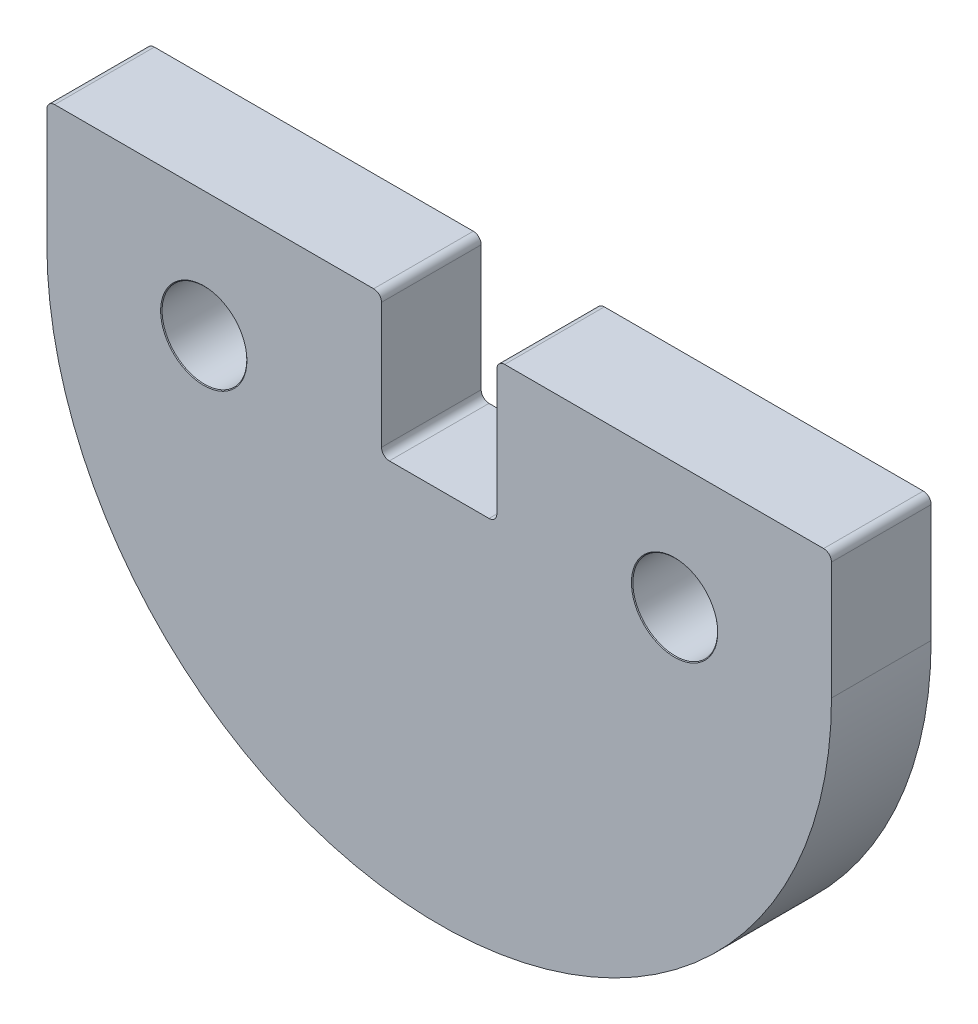
SolidWorks part; units mm, degrees
material "MDF"
ref_plane "Front Plane" through (0, 0, 0) normal (0, 0, 1) x (1, 0, 0)
ref_plane "Top Plane" through (0, 0, 0) normal (0, 1, 0) x (1, 0, 0)
ref_plane "Right Plane" through (0, 0, 0) normal (1, 0, 0) x (0, 0, -1)
sketch "Sketch1" plane through (0, 0, 0) normal (0, 0, 1) x (1, 0, 0)
  line L0 (-12.5, 0) -> (12.5, 0) construction
  line L1 (0, -1000) -> (0, 49000) construction
  line L2 (-12.5, 0) -> (12.5, 0) construction
  line L3 (-12.5, 0) -> (-12.5, 4)
  line L4 (-12.5, 4) -> (12.5, 4)
  line L5 (12.5, 0) -> (12.5, 4)
  line L7 (-1.8375, 4) -> (1.8375, 4)
  line L8 (-1.8375, 4) -> (-1.8375, -0.5)
  line L9 (-1.8375, -0.5) -> (1.8375, -0.5)
  line L10 (1.8375, 4) -> (1.8375, -0.5)
  arc A0 (-12.5, 0) -> (12.5, 0) centre (0, 0) ccw
  point P6 (-7.5, 0)
  point P7 (7.5, 0)
  dimension "D1" = 12.5
  dimension "D2" = 15
  dimension "D3" = 4
  dimension "D4" = 4.5
  dimension "D5" = 3.675
extrude "Boss-Extrude1" add sketch "Sketch1" along normal blind 3.175 contours L3 A0 L5 L4 L10 L9 L8
sketch "Sketch2" plane through (0, 0, 3.175) normal (0, 0, 1) x (1, 0, 0)
  point P0 (-7.5, 0)
  point P3 (7.5, 0)
hole_wizard "M2.5 Clearance Hole1" positions "Sketch2" profile "Sketch3" hole size "M2.5" standard "ANSI Metric" end condition through all
sketch "Sketch3" plane through (-7.5, 0, 3.175) normal (1, 0, 0) x (0, -1, 0)
  line L0 (0, 0) -> (0, 3.175)
  line L1 (0, 3.175) -> (1.35, 3.175)
  line L2 (1.35, 3.175) -> (1.35, 0.021)
  line L3 (1.35, 0.021) -> (1.375, 0)
  line L5 (1.375, 0) -> (0, 0)
  line L6 (-1.35, 0.021) -> (-1.375, 0) construction
  line L11 (0, -6.35) -> (0, 107.95) construction
  dimension "Thru Hole Dia." = 2.7
  dimension "Thru Hole Depth" = 3.175
  dimension "Near C'Sink Dia." = 2.75
  dimension "Near C'Sink Angle" = 100
fillet "Fillet1" radius 0.25 6 edges at (12.5, 4, 1.5875) (-1.8375, -0.5, 1.5875) (1.8375, -0.5, 1.5875) (1.8375, 4, 1.5875) (-1.8375, 4, 1.5875) (-12.5, 4, 1.5875)
